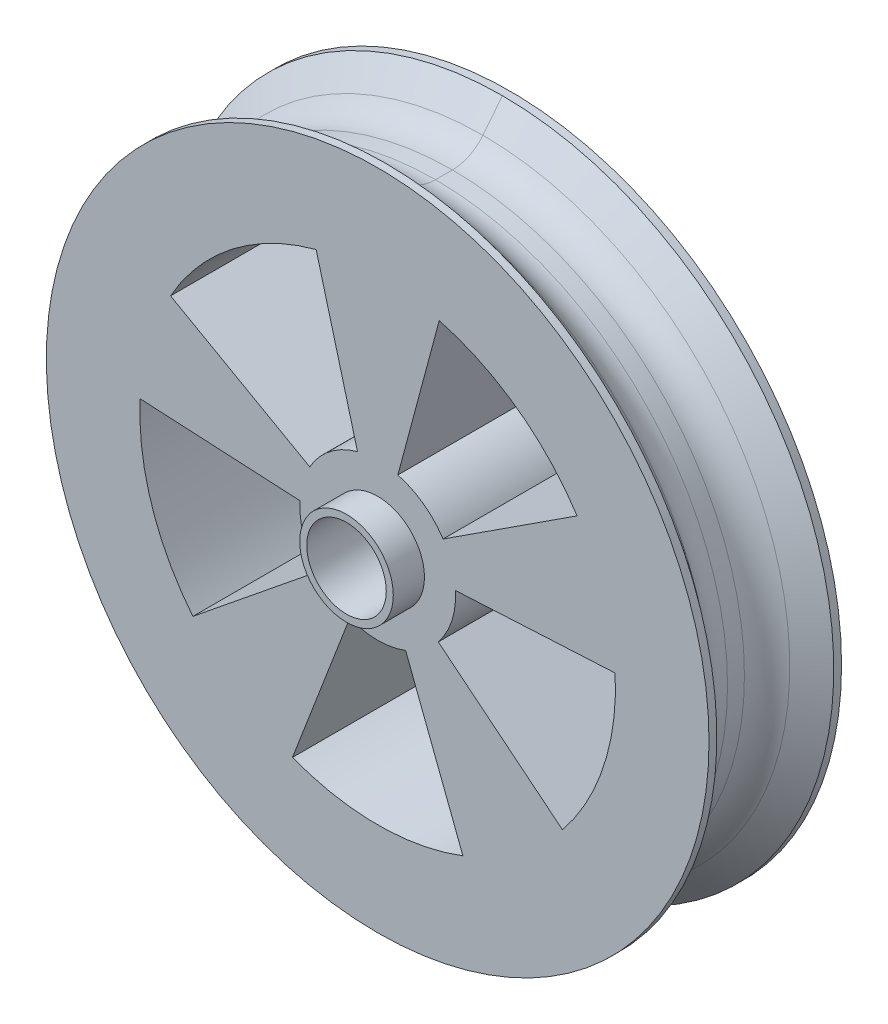
SolidWorks part; units mm, degrees
ref_plane "Front Plane" through (0, 0, 0) normal (0, 0, 1) x (1, 0, 0)
ref_plane "Top Plane" through (0, 0, 0) normal (0, 1, 0) x (1, 0, 0)
ref_plane "Right Plane" through (0, 0, 0) normal (1, 0, 0) x (0, 0, -1)
sketch "Sketch1" plane through (0, 0, 0) normal (0, 0, 1) x (1, 0, 0)
  circle A0 centre (0, 0) radius 42.5
  dimension "D1" = 85
extrude "Boss-Extrude1" add sketch "Sketch1" along normal blind 17
sketch "Sketch3" plane through (0, 0, 17) normal (0, 0, 1) x (1, 0, 0)
  line L5 (0, 0) -> (-7.894, 29.4607)
  line L6 (0, 0) -> (7.894, 29.4607)
  line L7 (0, 0) -> (25.5795, 16.6115)
  line L8 (0, 0) -> (30.4582, 1.5962)
  line L9 (0, 0) -> (23.703, -19.1943)
  line L10 (0, 0) -> (10.9302, -28.4742)
  line L11 (0, 0) -> (-10.9302, -28.4742)
  line L12 (0, 0) -> (-23.703, -19.1943)
  line L13 (0, 0) -> (-26.5706, 14.9751)
  line L14 (0, 0) -> (-30.4582, 1.5962)
  circle A0 centre (0, 0) radius 10
  circle A1 centre (0, 0) radius 30.5
extrude "Cut-Extrude3" cut sketch "Sketch3" against normal blind 17 contours L5 A1 L13 A0 | L7 A1 L6 A0 | L9 A1 L8 A0 | L11 A1 L10 A0 | L14 A1 L12 A0
sketch "Sketch4" plane through (0, 0, 17) normal (0, 0, 1) x (1, 0, 0)
  circle A0 centre (0, 0) radius 5.1
  dimension "D1" = 10.2
extrude "Cut-Extrude4" cut sketch "Sketch4" against normal blind 17
sketch "Sketch5" plane through (0, 0, 17) normal (0, 0, 1) x (1, 0, 0)
  circle A0 centre (0, 0) radius 6
  circle A1 centre (0, 0) radius 5.1
  circle A3 centre (0, 0) radius 5.1 construction
  dimension "D1" = 12
extrude "Boss-Extrude2" add sketch "Sketch5" along normal blind 4
sketch "Sketch6" plane through (0, 0, 0) normal (0, 0, -1) x (-1, 0, 0)
  circle A0 centre (0, 0) radius 6
  circle A1 centre (0, 0) radius 5.1
  circle A2 centre (0, 0) radius 5.1 construction
  dimension "D1" = 12
extrude "Boss-Extrude3" add sketch "Sketch6" along normal blind 4
sketch "Sketch10" plane through (0, 0, 0) normal (1, 0, 0) x (0, 0, -1)
  line L4 (0, 0) -> (45.792, 0)
  line L5 (-8.5, 42.5) -> (-8.5, 37.459)
  line L6 (0, 42.5) -> (-17, 42.5) construction
  line L11 (-5, 37.459) -> (-1, 42.5)
  line L12 (-8.5, 37.459) -> (-12, 37.459)
  line L13 (-12, 37.459) -> (-16, 42.5)
  line L14 (-16, 42.5) -> (-8.5, 42.5)
  line L15 (-8.5, 37.459) -> (-5, 37.459)
  line L16 (-8.5, 42.5) -> (-1, 42.5)
  dimension "D1" = 3.5
  dimension "D2" = 3.5
  dimension "D3" = 7.5
  dimension "D4" = 7.5
revolve "Cut-Revolve1" cut sketch "Sketch10" angle 360 about L4
fillet "Fillet1" radius 5 1 edges at (37.459, 0, 5)
fillet "Fillet2" radius 5 1 edges at (37.459, 0, 12)
split line "Split Line1"
